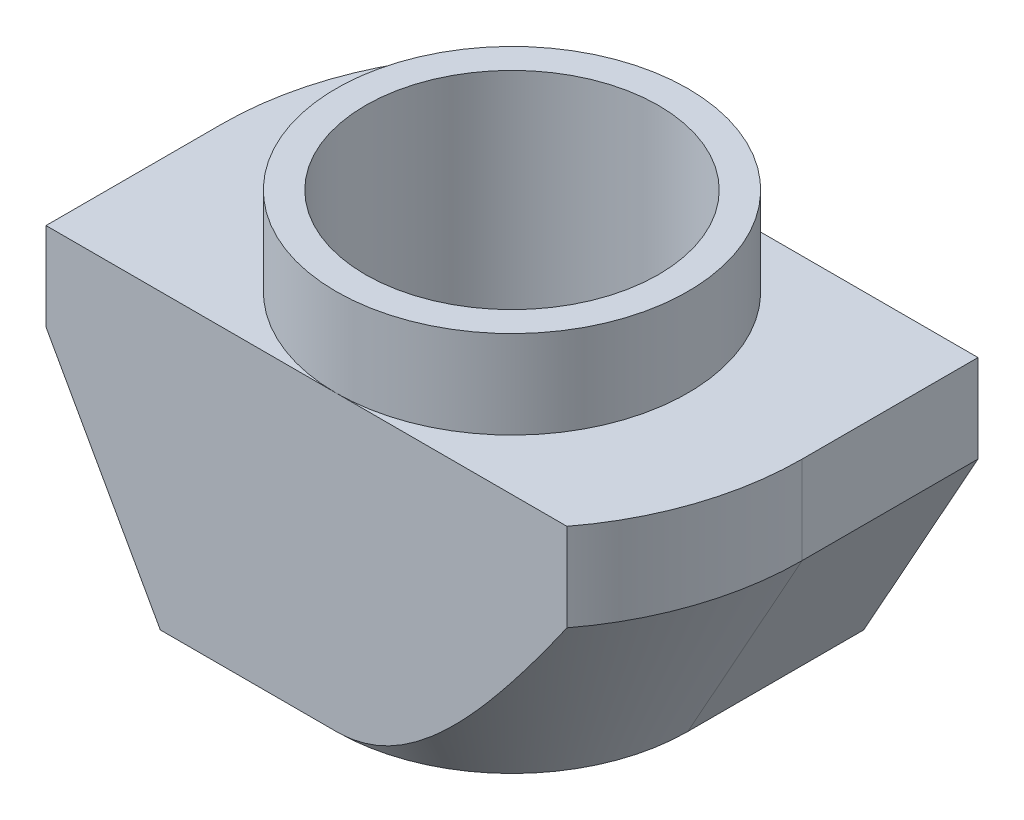
SolidWorks part; units mm, degrees
material "Сталь 20  ГОСТ 1050-2013"
ref_plane "Спереди" through (0, 0, 0) normal (0, 0, 1) x (1, 0, 0)
ref_plane "Сверху" through (0, 0, 0) normal (0, 1, 0) x (1, 0, 0)
ref_plane "Справа" through (0, 0, 0) normal (1, 0, 0) x (0, 0, -1)
sketch "Эскиз1" plane through (0, 0, 0) normal (0, 0, 1) x (1, 0, 0)
  line L0 (3, 0) -> (-3, 0)
  line L1 (-3, 0) -> (-3, -1.5)
  line L2 (-3, -1.5) -> (-4.95, -1.5)
  line L3 (-4.95, -1.5) -> (-4.95, -6.5)
  line L4 (-4.95, -6.5) -> (4.95, -6.5)
  line L5 (0, -6.5) -> (0, 0) construction
  line L6 (4.95, -1.5) -> (4.95, -6.5)
  line L7 (3, -1.5) -> (4.95, -1.5)
  line L8 (3, 0) -> (3, -1.5)
  dimension "D1" = 6
  dimension "D2" = 9.9
  dimension "D3" = 6.5
  dimension "D4" = 1.5
extrude "Бобышка-Вытянуть1" add sketch "Эскиз1" along normal mid plane 6
hole_wizard "Отверстие обработанное метчиком M61" positions "Эскиз2" profile "Эскиз3" tap size "M6" standard "ISO" end condition up to next
sketch "Эскиз2" plane through (0, 0, 0) normal (0, 1, 0) x (1, 0, 0)
  point P0 (0, 0)
cosmetic thread "Отверстие резьбы1" parameters "D2"=6
sketch "Эскиз3" plane through (0, 0, 0) normal (1, 0, 0) x (0, 0, 1)
  line L0 (0, 0) -> (0, 6.5)
  line L1 (0, 6.5) -> (2.5, 6.5)
  line L2 (2.5, 6.5) -> (2.5, 0)
  line L5 (2.5, 0) -> (0, 0)
  line L11 (0, -6.35) -> (0, 107.95) construction
  dimension "Диаметр проходного сверла" = 5
  dimension "Глубина проходного сверла" = 6.5
sketch "Эскиз4" plane through (0, 0, 0) normal (0, 1, 0) x (1, 0, 0)
  line L8 (-3, -3) -> (-3, 3) construction
  circle A2 centre (0, 0) radius 3
extrude "Вырез-Вытянуть1" cut sketch "Эскиз4" against normal up to surface (1.5 mm away) flip side to cut up to face at (-3.975, -1.5, 0)
sketch "Эскиз5" plane through (0, -1.5, 0) normal (0, 1, 0) x (1, 0, 0)
  line L0 (-4.95, 0) -> (-4.95, 3)
  line L1 (-4.95, -3) -> (-4.95, 3) construction
  line L2 (-4.95, 3) -> (-3.9373, 3)
  line L3 (0, 3) -> (-4.95, 3) construction
  line L4 (4.95, 0) -> (4.95, -3)
  line L5 (4.95, -3) -> (4.95, 3) construction
  line L6 (4.95, -3) -> (3.9373, -3)
  line L7 (4.95, -3) -> (0, -3) construction
  arc A0 (-3.9373, 3) -> (-4.95, 0) centre (0, 0) ccw
  arc A2 (4.95, 0) -> (3.9373, -3) centre (0, 0) cw
extrude "Вырез-Вытянуть2" cut sketch "Эскиз5" against normal through all
sketch "Эскиз6" plane through (0, 0, 3) normal (0, 0, 1) x (1, 0, 0)
  line L0 (-4.95, -3) -> (-4.95, -6.5)
  line L1 (-4.95, -1.5) -> (-4.95, -6.5) construction
  line L2 (-4.95, -6.5) -> (-3, -6.5)
  line L3 (-4.95, -6.5) -> (3.9373, -6.5) construction
  line L4 (-3, -6.5) -> (-4.95, -3)
  line L5 (0, -1.5) -> (-4.95, -1.5) construction
  line L7 (-3, 0) -> (-3, -1.5) construction
  point P10 (0, 0)
  dimension "D1" = 1.5
sketch "Эскиз7" plane through (0, -6.5, 0) normal (0, -1, 0) x (1, 0, 0)
  line L0 (0, 4.95) -> (-4.95, 4.95)
  line L1 (-4.95, 4.95) -> (-4.95, 0)
  line L2 (0, -4.95) -> (4.95, -4.95)
  line L3 (4.95, -4.95) -> (4.95, 0)
  arc A0 (-4.95, 0) -> (0, -4.95) centre (0, 0) ccw
  arc A1 (4.95, 0) -> (0, 4.95) centre (0, 0) ccw
sweep "Вырез-По траектории1" cut profiles "Эскиз6" path "Эскиз7"
